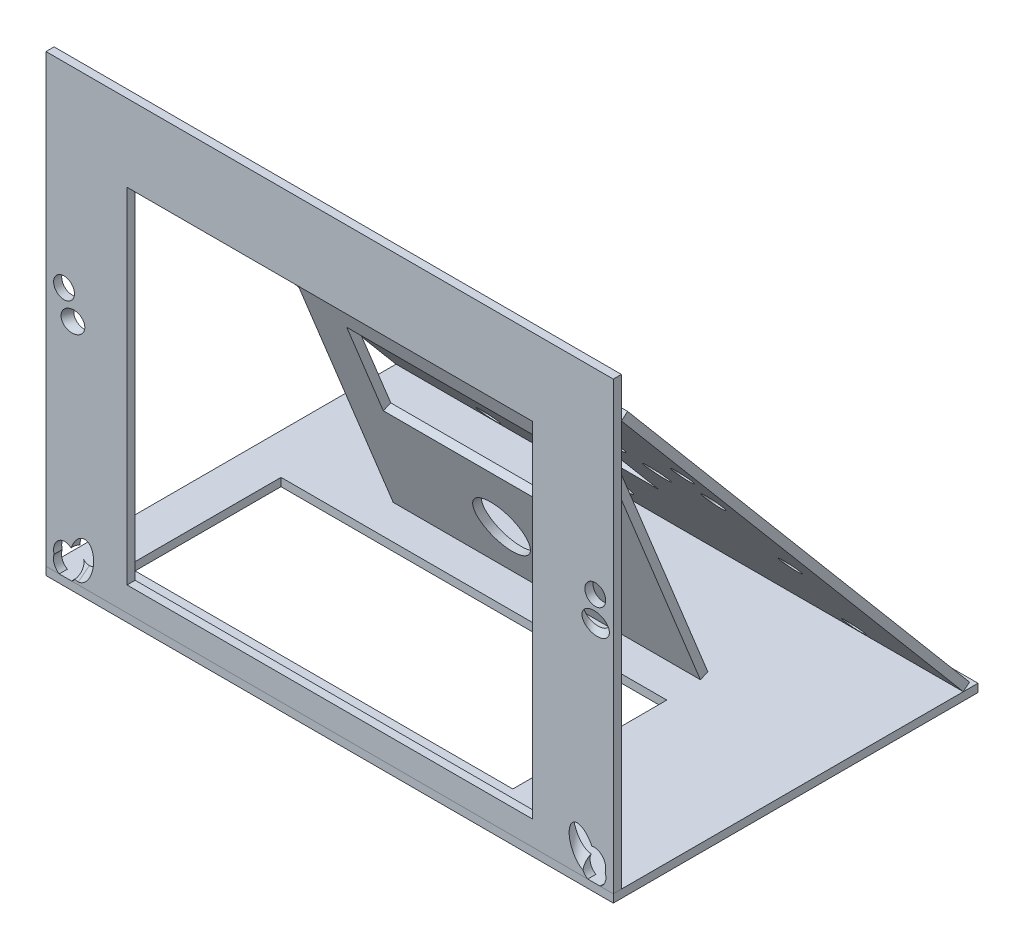
SolidWorks part; units mm, degrees
ref_plane "Front Plane" through (0, 0, 0) normal (0, 0, 1) x (1, 0, 0)
ref_plane "Top Plane" through (0, 0, 0) normal (0, 1, 0) x (1, 0, 0)
ref_plane "Right Plane" through (0, 0, 0) normal (1, 0, 0) x (0, 0, -1)
sketch "Sketch1" plane through (0, 0, 0) normal (0, 1, 0) x (1, 0, 0)
  line L0 (-350, 0) -> (-350, -10)
  line L1 (350, 440) -> (-350, 440)
  line L2 (350, 440) -> (350, 0)
  line L3 (350, 0) -> (-350, 0) construction
  line L4 (-350, 440) -> (-350, 0)
  line L5 (-350, -10) -> (350, -10)
  line L6 (350, -10) -> (350, 0)
  dimension "D1" = 450
  dimension "D2" = 700
  dimension "D3" = 10
extrude "Boss-Extrude1" add sketch "Sketch1" against normal blind 10
sketch "Sketch3" plane through (0, 0, 0) normal (0, 0, 1) x (1, 0, 0)
  line L1 (-350, 0) -> (350, 0)
  line L2 (-350, 0) -> (-350, 550)
  line L3 (-350, 550) -> (350, 550)
  line L4 (350, 0) -> (350, 550)
  dimension "D1" = 550
extrude "Boss-Extrude3" add sketch "Sketch3" along normal blind 10 separate body
ref_plane "Plane1" through (0, 207.9119, -246.5377) normal (0, -0.6447, 0.7645) x (0.6592, 0.5749, 0.4848)
sketch "Sketch4" plane through (0, 207.9119, -246.5377) normal (0, -0.6447, 0.7645) x (0.6592, 0.5749, 0.4848)
  line L1 (-435.2335, 83.9196) -> (26.1856, -442.476)
  line L2 (56.866, 515.276) -> (518.2851, -11.1197)
  line L3 (56.866, 515.276) -> (518.2851, -11.1197)
  line L4 (518.2851, -11.1197) -> (26.1856, -442.476)
  line L5 (56.866, 515.276) -> (-435.2335, 83.9196)
  circle A0 centre (218.2649, 31.0894) radius 22.86 construction
  circle A1 centre (112.9185, 151.2706) radius 22.86
  circle A2 centre (112.9185, 151.2706) radius 22.86
  circle A3 centre (164.269, 92.689) radius 22.86 construction
  circle A4 centre (60.2285, 211.3803) radius 22.86 construction
  circle A5 centre (218.2649, 31.0894) radius 22.86
  circle A6 centre (164.269, 92.689) radius 22.86
  circle A7 centre (60.2285, 211.3803) radius 22.86
  circle A189 centre (-340.5314, 1.0849) radius 12.7
  circle A190 centre (-43.5305, -337.7394) radius 12.7
  ellipse E0 centre (-340.5314, 1.0849) end of major axis (-348.5467, -14.0261) minor radius 12.7
  ellipse E1 centre (-340.5314, 1.0849) end of major axis (-348.5467, -14.0261) minor radius 12.7 construction
  ellipse E2 centre (-219.3301, 185.7304) end of major axis (-216.3849, 198.4621) minor radius 12.7
  ellipse E3 centre (-219.3301, 185.7304) end of major axis (-216.3849, 198.4621) minor radius 12.7
  ellipse E4 centre (-43.5305, -337.7394) end of major axis (-59.5612, -343.7063) minor radius 12.7
  ellipse E5 centre (-43.5305, -337.7394) end of major axis (-59.5612, -343.7063) minor radius 12.7 construction
  ellipse E6 centre (155.4002, -241.7691) end of major axis (168.408, -240.5169) minor radius 12.7
  ellipse E7 centre (155.4002, -241.7691) end of major axis (168.408, -240.5169) minor radius 12.7
  ellipse E12 centre (-99.9904, 314.0858) end of major axis (-90.3613, 327.8787) minor radius 12.7
  ellipse E13 centre (-99.9904, 314.0858) end of major axis (-90.3613, 327.8787) minor radius 12.7
  ellipse E14 centre (298.2818, -140.2708) end of major axis (313.2173, -132.5314) minor radius 12.7
  ellipse E15 centre (298.2818, -140.2708) end of major axis (313.2173, -132.5314) minor radius 12.7
  spline S0 degree 3 poles (-63.5133, 365.2118) (-63.7416, 366.4908) (-63.8118, 367.344) (-63.8022, 368.6245) (-63.7797, 369.0515) (-63.696, 369.9056) (-63.6342, 370.3349) (-63.3922, 371.6057) (-63.1573, 372.4278) (-62.6978, 373.6245) (-62.5267, 374.0173) (-62.1476, 374.7902) (-61.9388, 375.1713) (-61.269, 376.2725) (-60.7615, 376.9588) (-59.9084, 377.9161) (-59.6086, 378.223) (-58.9768, 378.8116) (-58.6462, 379.0915) (-57.6269, 379.875) (-56.9047, 380.3285) (-55.7554, 380.902) (-55.36, 381.0757) (-54.5511, 381.3831) (-54.1423, 381.515) (-52.9035, 381.8469) (-52.0609, 381.9835) (-50.7706, 382.0545) (-50.3351, 382.0553) (-49.4769, 382.0109) (-48.6261, 381.9212) (-47.79, 381.7415) (-46.9614, 381.516) (-46.5484, 381.3793) (-45.3437, 380.9061) (-44.586, 380.5089) (-43.5158, 379.794) (-43.1687, 379.5344) (-42.5048, 378.9802) (-42.1901, 378.6876) (-41.2956, 377.7656) (-40.7642, 377.0909) (-39.8358, 375.6279) (-39.4524, 374.8613) (-38.9902, 373.6625) (-38.855, 373.2547) (-38.6229, 372.4224) (-38.5267, 371.9998) (-38.2998, 370.7322) (-38.228, 369.8797) (-38.237, 368.5904) (-38.2598, 368.1567) (-38.3442, 367.2986) (-38.4055, 366.8741) (-38.6451, 365.6136) (-38.8786, 364.7905) (-39.3419, 363.5824) (-39.5154, 363.1846) (-39.8935, 362.4138) (-40.0988, 362.0386) (-40.7634, 360.9438) (-41.2706, 360.2543) (-42.4214, 358.9614) (-43.0492, 358.3762) (-44.0626, 357.595) (-44.4128, 357.3504) (-45.1386, 356.894) (-45.5161, 356.6813) (-46.6757, 356.102) (-47.4745, 355.7979) (-48.7113, 355.4649) (-49.13, 355.3746) (-49.9809, 355.2373) (-50.4139, 355.1905) (-51.701, 355.1202) (-52.554, 355.1635) (-53.8258, 355.3663) (-54.251, 355.4577) (-55.0841, 355.6852) (-55.4913, 355.8207) (-56.2876, 356.1338) (-56.6767, 356.3115) (-57.4366, 356.7092) (-57.8089, 356.9302) (-58.8882, 357.6526) (-59.5449, 358.2029) (-60.7391, 359.434) (-61.2793, 360.1216) (-62.1979, 361.5703) (-62.5826, 362.336) (-63.0493, 363.5457) (-63.1855, 363.9578) (-63.4173, 364.79) (-63.5133, 365.2118) (-63.7416, 366.4908) (-63.8118, 367.344) knots -0.015625 -0.015625 0 0 0.03125 0.03125 0.046875 0.046875 0.0625 0.0625 0.09375 0.09375 0.109375 0.109375 0.125 0.125 0.15625 0.15625 0.171875 0.171875 0.1875 0.1875 0.21875 0.21875 0.234375 0.234375 0.25 0.25 0.28125 0.28125 0.296875 0.296875 0.3125 0.328125 0.328125 0.34375 0.34375 0.375 0.375 0.390625 0.390625 0.40625 0.40625 0.4375 0.4375 0.46875 0.46875 0.484375 0.484375 0.5 0.5 0.53125 0.53125 0.546875 0.546875 0.5625 0.5625 0.59375 0.59375 0.609375 0.609375 0.625 0.625 0.65625 0.65625 0.6875 0.6875 0.703125 0.703125 0.71875 0.71875 0.75 0.75 0.765625 0.765625 0.78125 0.78125 0.8125 0.8125 0.828125 0.828125 0.84375 0.84375 0.859375 0.859375 0.875 0.875 0.90625 0.90625 0.9375 0.9375 0.96875 0.96875 0.984375 0.984375 1 1 1.03125 1.03125 1.046875 only from (-63.5894, 365.6381) to (-63.5894, 365.6381)
  spline S1 degree 3 poles (-63.5133, 365.2118) (-63.7416, 366.4908) (-63.8118, 367.344) (-63.8022, 368.6245) (-63.7797, 369.0515) (-63.696, 369.9056) (-63.6342, 370.3349) (-63.3922, 371.6057) (-63.1573, 372.4278) (-62.6978, 373.6245) (-62.5267, 374.0173) (-62.1476, 374.7902) (-61.9388, 375.1713) (-61.269, 376.2725) (-60.7615, 376.9588) (-59.9084, 377.9161) (-59.6086, 378.223) (-58.9768, 378.8116) (-58.6462, 379.0915) (-57.6269, 379.875) (-56.9047, 380.3285) (-55.7554, 380.902) (-55.36, 381.0757) (-54.5511, 381.3831) (-54.1423, 381.515) (-52.9035, 381.8469) (-52.0609, 381.9835) (-50.7706, 382.0545) (-50.3351, 382.0553) (-49.4769, 382.0109) (-48.6261, 381.9212) (-47.79, 381.7415) (-46.9614, 381.516) (-46.5484, 381.3793) (-45.3437, 380.9061) (-44.586, 380.5089) (-43.5158, 379.794) (-43.1687, 379.5344) (-42.5048, 378.9802) (-42.1901, 378.6876) (-41.2956, 377.7656) (-40.7642, 377.0909) (-39.8358, 375.6279) (-39.4524, 374.8613) (-38.9902, 373.6625) (-38.855, 373.2547) (-38.6229, 372.4224) (-38.5267, 371.9998) (-38.2998, 370.7322) (-38.228, 369.8797) (-38.237, 368.5904) (-38.2598, 368.1567) (-38.3442, 367.2986) (-38.4055, 366.8741) (-38.6451, 365.6136) (-38.8786, 364.7905) (-39.3419, 363.5824) (-39.5154, 363.1846) (-39.8935, 362.4138) (-40.0988, 362.0386) (-40.7634, 360.9438) (-41.2706, 360.2543) (-42.4214, 358.9614) (-43.0492, 358.3762) (-44.0626, 357.595) (-44.4128, 357.3504) (-45.1386, 356.894) (-45.5161, 356.6813) (-46.6757, 356.102) (-47.4745, 355.7979) (-48.7113, 355.4649) (-49.13, 355.3746) (-49.9809, 355.2373) (-50.4139, 355.1905) (-51.701, 355.1202) (-52.554, 355.1635) (-53.8258, 355.3663) (-54.251, 355.4577) (-55.0841, 355.6852) (-55.4913, 355.8207) (-56.2876, 356.1338) (-56.6767, 356.3115) (-57.4366, 356.7092) (-57.8089, 356.9302) (-58.8882, 357.6526) (-59.5449, 358.2029) (-60.7391, 359.434) (-61.2793, 360.1216) (-62.1979, 361.5703) (-62.5826, 362.336) (-63.0493, 363.5457) (-63.1855, 363.9578) (-63.4173, 364.79) (-63.5133, 365.2118) (-63.7416, 366.4908) (-63.8118, 367.344) knots -0.015625 -0.015625 0 0 0.03125 0.03125 0.046875 0.046875 0.0625 0.0625 0.09375 0.09375 0.109375 0.109375 0.125 0.125 0.15625 0.15625 0.171875 0.171875 0.1875 0.1875 0.21875 0.21875 0.234375 0.234375 0.25 0.25 0.28125 0.28125 0.296875 0.296875 0.3125 0.328125 0.328125 0.34375 0.34375 0.375 0.375 0.390625 0.390625 0.40625 0.40625 0.4375 0.4375 0.46875 0.46875 0.484375 0.484375 0.5 0.5 0.53125 0.53125 0.546875 0.546875 0.5625 0.5625 0.59375 0.59375 0.609375 0.609375 0.625 0.625 0.65625 0.65625 0.6875 0.6875 0.703125 0.703125 0.71875 0.71875 0.75 0.75 0.765625 0.765625 0.78125 0.78125 0.8125 0.8125 0.828125 0.828125 0.84375 0.84375 0.859375 0.859375 0.875 0.875 0.90625 0.90625 0.9375 0.9375 0.96875 0.96875 0.984375 0.984375 1 1 1.03125 1.03125 1.046875 only from (-63.5894, 365.6381) to (-63.5894, 365.6381)
  spline S2 degree 3 poles (345.3418, -100.7935) (345.2113, -99.499) (345.219, -98.6428) (345.3649, -97.3681) (345.4361, -96.9448) (345.6244, -96.1015) (345.7413, -95.6839) (346.1518, -94.4639) (346.5065, -93.6853) (347.1572, -92.5685) (347.3947, -92.2042) (347.8992, -91.5079) (348.1673, -91.1738) (348.7339, -90.5327) (349.0324, -90.2258) (349.66, -89.639) (349.9907, -89.3579) (351.0146, -88.567) (351.7376, -88.1094) (352.8798, -87.5226) (353.2703, -87.3437) (354.0709, -87.02) (354.4792, -86.8762) (355.7106, -86.503) (356.5469, -86.329) (357.824, -86.1799) (358.2548, -86.1489) (359.119, -86.126) (359.5484, -86.1342) (360.8289, -86.2159) (361.6722, -86.3463) (362.9213, -86.6597) (363.3372, -86.7848) (364.1499, -87.0719) (364.5466, -87.2336) (365.7085, -87.7725) (366.4455, -88.2031) (367.491, -88.9627) (367.8297, -89.2358) (368.4702, -89.8079) (368.7741, -90.1085) (369.3495, -90.7385) (369.6208, -91.068) (370.1302, -91.7566) (370.3689, -92.1171) (371.0266, -93.2366) (371.3785, -94.0163) (371.7791, -95.235) (371.8913, -95.6495) (372.0713, -96.4956) (372.1381, -96.9238) (372.268, -98.204) (372.2629, -99.0595) (372.1171, -100.346) (372.0451, -100.7749) (371.8583, -101.6137) (371.7434, -102.0262) (371.4718, -102.8378) (371.315, -103.237) (370.9595, -104.0218) (370.7598, -104.4086) (370.111, -105.5245) (369.6093, -106.2179) (368.757, -107.1852) (368.4546, -107.4969) (367.8248, -108.0868) (367.4979, -108.365) (366.4826, -109.1512) (365.7598, -109.6112) (364.6065, -110.2047) (364.2134, -110.3846) (363.4182, -110.7064) (362.6117, -110.9912) (361.7826, -111.2033) (360.9422, -111.3787) (360.5144, -111.4482) (359.2281, -111.5979) (358.3732, -111.62) (357.0944, -111.5387) (356.6687, -111.4924) (355.8188, -111.3603) (355.3925, -111.2739) (354.1407, -110.9587) (353.3356, -110.6744) (352.1727, -110.1355) (351.7925, -109.9371) (351.0479, -109.5006) (350.6845, -109.2628) (349.6437, -108.5056) (349.0066, -107.9381) (348.1389, -106.9896) (347.8633, -106.6556) (347.3487, -105.96) (347.1119, -105.6016) (346.4615, -104.4956) (346.1073, -103.7174) (345.7015, -102.4853) (345.5882, -102.0658) (345.4087, -101.2208) (345.3418, -100.7935) (345.2113, -99.499) (345.219, -98.6428) knots -0.015625 -0.015625 0 0 0.03125 0.03125 0.046875 0.046875 0.0625 0.0625 0.09375 0.09375 0.109375 0.109375 0.125 0.125 0.140625 0.140625 0.15625 0.15625 0.1875 0.1875 0.203125 0.203125 0.21875 0.21875 0.25 0.25 0.265625 0.265625 0.28125 0.28125 0.3125 0.3125 0.328125 0.328125 0.34375 0.34375 0.375 0.375 0.390625 0.390625 0.40625 0.40625 0.421875 0.421875 0.4375 0.4375 0.46875 0.46875 0.484375 0.484375 0.5 0.5 0.53125 0.53125 0.546875 0.546875 0.5625 0.5625 0.578125 0.578125 0.59375 0.59375 0.625 0.625 0.640625 0.640625 0.65625 0.65625 0.6875 0.6875 0.703125 0.703125 0.71875 0.734375 0.734375 0.75 0.75 0.78125 0.78125 0.796875 0.796875 0.8125 0.8125 0.84375 0.84375 0.859375 0.859375 0.875 0.875 0.90625 0.90625 0.921875 0.921875 0.9375 0.9375 0.96875 0.96875 0.984375 0.984375 1 1 1.03125 1.03125 1.046875 only from (345.2983, -100.362) to (345.2983, -100.362)
  spline S3 degree 3 poles (345.3418, -100.7935) (345.2113, -99.499) (345.219, -98.6428) (345.3649, -97.3681) (345.4361, -96.9448) (345.6244, -96.1015) (345.7413, -95.6839) (346.1518, -94.4639) (346.5065, -93.6853) (347.1572, -92.5685) (347.3947, -92.2042) (347.8992, -91.5079) (348.1673, -91.1738) (348.7339, -90.5327) (349.0324, -90.2258) (349.66, -89.639) (349.9907, -89.3579) (351.0146, -88.567) (351.7376, -88.1094) (352.8798, -87.5226) (353.2703, -87.3437) (354.0709, -87.02) (354.4792, -86.8762) (355.7106, -86.503) (356.5469, -86.329) (357.824, -86.1799) (358.2548, -86.1489) (359.119, -86.126) (359.5484, -86.1342) (360.8289, -86.2159) (361.6722, -86.3463) (362.9213, -86.6597) (363.3372, -86.7848) (364.1499, -87.0719) (364.5466, -87.2336) (365.7085, -87.7725) (366.4455, -88.2031) (367.491, -88.9627) (367.8297, -89.2358) (368.4702, -89.8079) (368.7741, -90.1085) (369.3495, -90.7385) (369.6208, -91.068) (370.1302, -91.7566) (370.3689, -92.1171) (371.0266, -93.2366) (371.3785, -94.0163) (371.7791, -95.235) (371.8913, -95.6495) (372.0713, -96.4956) (372.1381, -96.9238) (372.268, -98.204) (372.2629, -99.0595) (372.1171, -100.346) (372.0451, -100.7749) (371.8583, -101.6137) (371.7434, -102.0262) (371.4718, -102.8378) (371.315, -103.237) (370.9595, -104.0218) (370.7598, -104.4086) (370.111, -105.5245) (369.6093, -106.2179) (368.757, -107.1852) (368.4546, -107.4969) (367.8248, -108.0868) (367.4979, -108.365) (366.4826, -109.1512) (365.7598, -109.6112) (364.6065, -110.2047) (364.2134, -110.3846) (363.4182, -110.7064) (362.6117, -110.9912) (361.7826, -111.2033) (360.9422, -111.3787) (360.5144, -111.4482) (359.2281, -111.5979) (358.3732, -111.62) (357.0944, -111.5387) (356.6687, -111.4924) (355.8188, -111.3603) (355.3925, -111.2739) (354.1407, -110.9587) (353.3356, -110.6744) (352.1727, -110.1355) (351.7925, -109.9371) (351.0479, -109.5006) (350.6845, -109.2628) (349.6437, -108.5056) (349.0066, -107.9381) (348.1389, -106.9896) (347.8633, -106.6556) (347.3487, -105.96) (347.1119, -105.6016) (346.4615, -104.4956) (346.1073, -103.7174) (345.7015, -102.4853) (345.5882, -102.0658) (345.4087, -101.2208) (345.3418, -100.7935) (345.2113, -99.499) (345.219, -98.6428) knots -0.015625 -0.015625 0 0 0.03125 0.03125 0.046875 0.046875 0.0625 0.0625 0.09375 0.09375 0.109375 0.109375 0.125 0.125 0.140625 0.140625 0.15625 0.15625 0.1875 0.1875 0.203125 0.203125 0.21875 0.21875 0.25 0.25 0.265625 0.265625 0.28125 0.28125 0.3125 0.3125 0.328125 0.328125 0.34375 0.34375 0.375 0.375 0.390625 0.390625 0.40625 0.40625 0.421875 0.421875 0.4375 0.4375 0.46875 0.46875 0.484375 0.484375 0.5 0.5 0.53125 0.53125 0.546875 0.546875 0.5625 0.5625 0.578125 0.578125 0.59375 0.59375 0.625 0.625 0.640625 0.640625 0.65625 0.65625 0.6875 0.6875 0.703125 0.703125 0.71875 0.734375 0.734375 0.75 0.75 0.78125 0.78125 0.796875 0.796875 0.8125 0.8125 0.84375 0.84375 0.859375 0.859375 0.875 0.875 0.90625 0.90625 0.921875 0.921875 0.9375 0.9375 0.96875 0.96875 0.984375 0.984375 1 1 1.03125 1.03125 1.046875 only from (345.2983, -100.362) to (345.2983, -100.362)
  dimension "D2" = 25.4
  dimension "D1" = 0
extrude "Boss-Extrude4" add sketch "Sketch4" against normal blind 10 separate body
sketch "Sketch5" plane through (0, 0, 0) normal (0, 0, -1) x (-1, 0, 0)
  line L0 (0, 0) -> (0, 481.8166) construction
  line L1 (350, 0) -> (-350, 0) construction
  line L2 (250, 30) -> (-250, 30)
  line L3 (250, 30) -> (250, 455)
  line L4 (250, 455) -> (-250, 455)
  line L5 (-250, 30) -> (-250, 455)
  line L6 (250, 30) -> (-250, 455) construction
  line L7 (250, 455) -> (-250, 30) construction
  line L8 (340.0766, 17.4928) -> (339.954, 17.8507)
  line L9 (-340.0766, 17.4928) -> (-339.954, 17.8507)
  circle A0 centre (-301.1828, 56.689) radius 12.7 construction
  circle A1 centre (299.1609, 56.4193) radius 12.7 construction
  arc A2 (315.0379, 22.539) -> (340.0766, 17.4928) centre (326.0828, 12.7) ccw
  arc A3 (-315.0379, 22.539) -> (-340.0766, 17.4928) centre (-326.0828, 12.7) cw
  ellipse E0 centre (326.0828, 12.7) end of major axis (313.0068, 12.7) minor radius 12.7
  ellipse E1 centre (326.0828, 12.7) end of major axis (313.0068, 12.7) minor radius 12.7 (316.4369, 21.2745) -> (338.8851, 15.2852) ccw construction
  ellipse E2 centre (327.7654, 23.513) end of major axis (331.8034, 9.4187) minor radius 12.7
  ellipse E3 centre (327.7654, 23.513) end of major axis (331.8034, 9.4187) minor radius 12.7 (339.954, 17.8507) -> (315.0379, 22.539) ccw
  ellipse E4 centre (327.7654, 308.7) end of major axis (340.6246, 308.7) minor radius 12.7
  ellipse E5 centre (327.7654, 308.7) end of major axis (340.6246, 308.7) minor radius 12.7
  ellipse E6 centre (-326.0828, 12.7) end of major axis (-313.0068, 12.7) minor radius 12.7
  ellipse E7 centre (-326.0828, 12.7) end of major axis (-313.0068, 12.7) minor radius 12.7 (-338.8851, 15.2852) -> (-316.4369, 21.2745) ccw construction
  ellipse E8 centre (-327.7654, 23.513) end of major axis (-331.8034, 9.4187) minor radius 12.7
  ellipse E9 centre (-327.7654, 23.513) end of major axis (-331.8034, 9.4187) minor radius 12.7 (-315.0379, 22.539) -> (-339.954, 17.8507) ccw
  ellipse E10 centre (-327.7654, 308.7) end of major axis (-340.6246, 308.7) minor radius 12.7
  ellipse E11 centre (-327.7654, 308.7) end of major axis (-340.6246, 308.7) minor radius 12.7
  ellipse E13 centre (-301.1828, 56.689) end of major axis (-310.0263, 33.2898) minor radius 14.2 (-287.4745, 75.6336) -> (-305.6128, 75.6336) ccw construction
  ellipse E15 centre (299.1609, 56.4193) end of major axis (305.2844, 31.9315) minor radius 14.2 (305.0648, 75.6336) -> (286.8161, 75.6336) ccw construction
  point P92 (0, 242.5)
  dimension "D1" = 25.4
  dimension "D2" = 30
  dimension "D3" = 425
  dimension "D4" = 500
extrude "Cut-Extrude1" cut sketch "Sketch5" against normal through all
ref_plane "Plane3" through (249.9608, 192.2191, -109.9049) normal (-0.291, 0.7701, -0.5677) x (0.9567, 0.2343, -0.1727)
sketch "Sketch11" plane through (249.9608, 192.2191, -109.9049) normal (-0.291, 0.7701, -0.5677) x (0.9567, 0.2343, -0.1727)
  line L0 (0.4499, 14.1929) -> (0.25, 14.1978)
  arc A3 (0.25, 14.1978) -> (0.4499, 14.1929) centre (0, 0) ccw
  arc A4 (0.25, 14.1978) -> (0.4499, 14.1929) centre (0, 0) ccw
extrude "Cut-Extrude5" cut sketch "Sketch11" against normal through all and the other way through all
ref_plane "Plane4" through (-265.0386, 192.8743, -105.7083) normal (-0.2006, -0.8021, 0.5626) x (-0.9797, 0.1642, -0.1152)
sketch "Sketch12" plane through (-265.0386, 192.8743, -105.7083) normal (-0.2006, -0.8021, 0.5626) x (-0.9797, 0.1642, -0.1152)
  line L0 (-0.4219, 14.1937) -> (-0.222, 14.1983)
  arc A0 (-0.4219, 14.1937) -> (-0.222, 14.1983) centre (0, 0) ccw
  arc A1 (-0.4219, 14.1937) -> (-0.222, 14.1983) centre (0, 0) ccw
extrude "Cut-Extrude6" cut sketch "Sketch12" against normal through all and the other way through all
sketch "Sketch6" plane through (0, 0, 0) normal (0, 1, 0) x (1, 0, 0)
  line L0 (-350, 282.6445) -> (350, 282.6445)
  line L1 (-350, 7.6445) -> (-350, 429.52) construction
  line L2 (350, 429.52) -> (350, 7.6445) construction
  line L3 (350, 7.6445) -> (-350, 7.6445) construction
  dimension "D1" = 275
ref_plane "Plane5" through (249.9608, 292.2795, -78.9221) normal (-0.656, 0.1201, -0.7451) x (-0.7548, -0.1044, 0.6477)
sketch "Sketch13" plane through (249.9608, 292.2795, -78.9221) normal (-0.656, 0.1201, -0.7451) x (-0.7548, -0.1044, 0.6477)
  circle A0 centre (0, 0) radius 12.7
  dimension "D1" = 25.4
extrude "Cut-Extrude7" cut sketch "Sketch13" against normal through all and the other way through all
ref_plane "Plane6" through (-265.0386, 291.8405, -79.5184) normal (-0.4962, -0.1313, 0.8582) x (0.8682, -0.0751, 0.4905)
sketch "Sketch14" plane through (-265.0386, 291.8405, -79.5184) normal (-0.4962, -0.1313, 0.8582) x (0.8682, -0.0751, 0.4905)
  circle A0 centre (0, 0) radius 12.7
  dimension "D1" = 25.4
extrude "Cut-Extrude8" cut sketch "Sketch14" against normal through all and the other way through all
ref_plane "Plane2" through (0, 98.1707, -242.981) normal (0, 0.3746, -0.9272) x (-1, 0, 0)
sketch "Sketch7" plane through (0, 98.1707, -242.981) normal (0, 0.3746, -0.9272) x (-1, 0, 0)
  line L1 (-400, 239.6936) -> (-312.9923, 239.6936)
  line L2 (203, -100.757) -> (-176, -100.757)
  line L3 (203, -100.757) -> (203, 235.9476)
  line L5 (-176, -100.757) -> (-176, 235.9476)
  line L6 (-177.4441, 235.9476) -> (293.4176, 235.9476)
  line L7 (312.9923, 239.6936) -> (400, 239.6936)
  line L8 (-293.4176, 235.9476) -> (-185.7896, 235.9476)
  line L9 (-176, 235.9476) -> (203, 235.9476)
  point P3 (0, 0)
  dimension "D1" = 203
  dimension "D2" = 176
extrude "Boss-Extrude5" add sketch "Sketch7" against normal blind 10
sketch "Sketch8" plane through (0, 0, 0) normal (0, 0, 1) x (1, 0, 0)
  arc A2 (-41.697, 36.4138) -> (-41.697, 102.5433) centre (-41.697, 69.4786) ccw
  arc A3 (-41.697, 102.5433) -> (-41.697, 36.4138) centre (-41.697, 69.4786) ccw
  arc A4 (-41.697, 36.4138) -> (-41.697, 102.5433) centre (-41.697, 69.4786) ccw
  arc A5 (-41.697, 102.5433) -> (-41.697, 36.4138) centre (-41.697, 69.4786) ccw
  dimension "D1" = 0
extrude "Cut-Extrude2" cut sketch "Sketch8" against normal through all
sketch "Sketch9" plane through (0, 0, 0) normal (0, 1, 0) x (1, 0, 0)
  line L0 (-350, 7.6445) -> (-350, 429.52) construction
  line L1 (-300, 40) -> (176, 40)
  line L2 (-300, 40) -> (-300, 230)
  line L3 (-300, 230) -> (176, 230)
  line L4 (176, 40) -> (176, 230)
  line L5 (350, -10) -> (-350, -10) construction
  dimension "D1" = 50
  dimension "D2" = 50
  dimension "D3" = 176
  dimension "D4" = 190
extrude "Cut-Extrude3" cut sketch "Sketch9" against normal blind 10
sketch "Sketch10" plane through (0, 94.4246, -233.7091) normal (0, -0.3746, 0.9272) x (1, 0, 0)
  line L0 (-203, -100.757) -> (-203, 235.9476) construction
  line L1 (-153, 65.3661) -> (126, 65.3661)
  line L2 (-153, 65.3661) -> (-153, 185.9476)
  line L3 (-153, 185.9476) -> (126, 185.9476)
  line L4 (126, 65.3661) -> (126, 185.9476)
  line L5 (176, 235.9476) -> (176, -100.757) construction
  line L6 (-203, 235.9476) -> (176, 235.9476) construction
  point P10 (-41.697, 15.3661)
  dimension "D1" = 50
  dimension "D2" = 50
  dimension "D3" = 50
  dimension "D4" = 50
extrude "Cut-Extrude4" cut sketch "Sketch10" against normal through all
